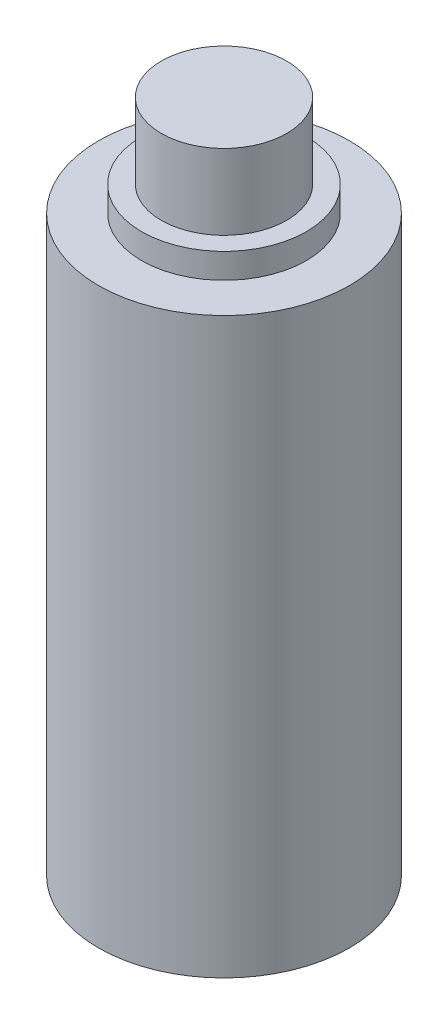
SolidWorks part; units mm, degrees
material "6061-T6 (SS)"
ref_plane "Front Plane" through (0, 0, 0) normal (0, 0, 1) x (1, 0, 0)
ref_plane "Top Plane" through (0, 0, 0) normal (0, 1, 0) x (1, 0, 0)
ref_plane "Right Plane" through (0, 0, 0) normal (1, 0, 0) x (0, 0, -1)
sketch "Sketch1" plane through (0, 0, 0) normal (0, 1, 0) x (1, 0, 0)
  circle A0 centre (0, 0) radius 4
  dimension "D1" = 8
extrude "Boss-Extrude1" add sketch "Sketch1" along normal blind 18.288
sketch "Sketch2" plane through (0, 18.288, 0) normal (0, 1, 0) x (1, 0, 0)
  circle A0 centre (0, 0) radius 2.625
  dimension "D1" = 5.25
extrude "Boss-Extrude2" add sketch "Sketch2" along normal blind 0.8
sketch "Sketch3" plane through (0, 19.088, 0) normal (0, 1, 0) x (1, 0, 0)
  circle A0 centre (0, 0) radius 2
  dimension "D1" = 4
extrude "Boss-Extrude3" add sketch "Sketch3" along normal blind 2.4
